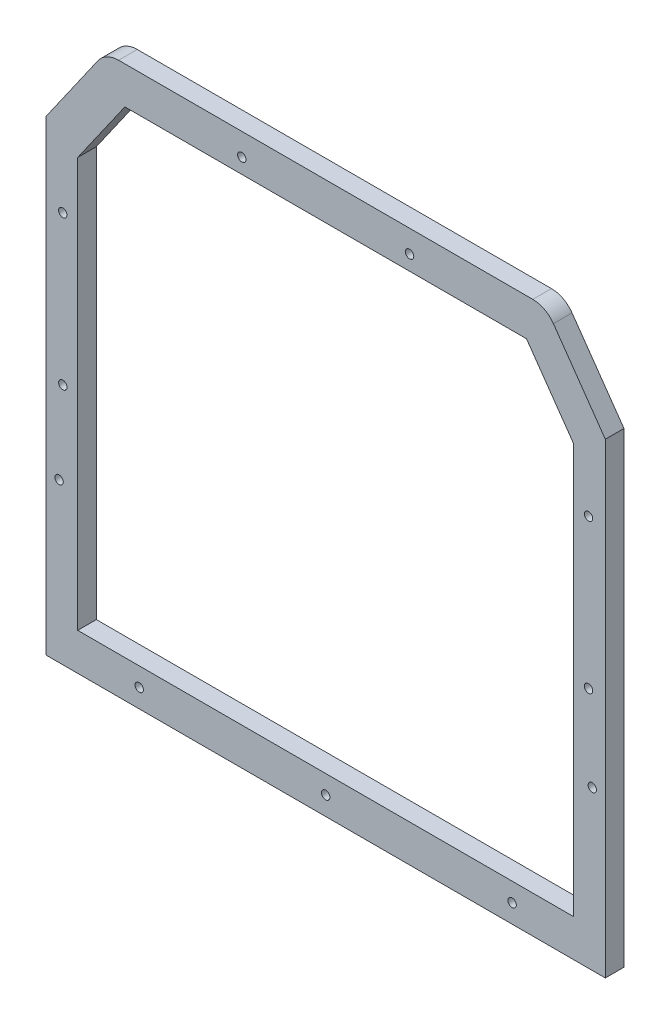
SolidWorks part; units mm, degrees
material "ABS"
ref_plane "Alzado" through (0, 0, 0) normal (0, 0, 1) x (1, 0, 0)
ref_plane "Planta" through (0, 0, 0) normal (0, 1, 0) x (1, 0, 0)
ref_plane "Vista lateral" through (0, 0, 0) normal (1, 0, 0) x (0, 0, -1)
sketch "Croquis1" plane through (0, 0, 0) normal (0, 0, 1) x (1, 0, 0)
  line L0 (303.5586, 129.4867) -> (275.1559, 170.0499)
  line L1 (264.0973, 175.8067) -> (41.9027, 175.8067)
  line L2 (30.8441, 170.0499) -> (2.4414, 129.4867)
  line L3 (0, 121.7435) -> (0, 0)
  line L5 (20, 0) -> (20, 119.694)
  line L6 (20, 119.694) -> (45.2863, 155.8067)
  line L7 (45.2863, 155.8067) -> (260.7137, 155.8067)
  line L8 (260.7137, 155.8067) -> (286, 119.694)
  line L9 (286, 119.694) -> (286, 0)
  line L11 (306, 0) -> (306, 121.7435)
  line L12 (0, 0) -> (0, -120)
  line L13 (0, -120) -> (306, -120)
  line L14 (306, -120) -> (306, 0)
  line L15 (20, 0) -> (20, -100)
  line L16 (20, -100) -> (286, -100)
  line L17 (286, -100) -> (286, 0)
  arc A0 (306, 121.7435) -> (303.5586, 129.4867) centre (292.5, 121.7435) ccw
  arc A1 (275.1559, 170.0499) -> (264.0973, 175.8067) centre (264.0973, 162.3067) ccw
  arc A2 (41.9027, 175.8067) -> (30.8441, 170.0499) centre (41.9027, 162.3067) ccw
  arc A3 (2.4414, 129.4867) -> (0, 121.7435) centre (13.5, 121.7435) ccw
  dimension "D5" = 13.5
  dimension "D6" = 13.5
  dimension "D7" = 20
  dimension "D1" = 222.1947
  dimension "D2" = 306
  dimension "D3" = 121.7435
  dimension "D4" = 54.0632
  dimension "D8" = 20
  dimension "D9" = 20
  dimension "D10" = 20
  dimension "D11" = 20
  dimension "D12" = 28.4027
  dimension "D13" = 30.8441
  dimension "D14" = 20
  dimension "D15" = 125
  dimension "D16" = 222.1947
  dimension "D17" = 120
extrude "Saliente-Extruir1" add sketch "Croquis1" along normal blind 10
sketch "Croquis2" plane through (0, 0, 10) normal (0, 0, 1) x (1, 0, 0)
  line L0 (108, 163.8067) -> (198, 163.8067) construction
  line L1 (264.0973, 175.8067) -> (41.9027, 175.8067) construction
  line L2 (260.7137, 155.8067) -> (45.2863, 155.8067) construction
  line L3 (20, 119.694) -> (20, -100) construction
  line L4 (286, -100) -> (286, 119.694) construction
  line L5 (0, 50) -> (306, 50) construction
  line L6 (0, 121.7435) -> (0, -120) construction
  line L7 (306, -120) -> (306, 121.7435) construction
  circle A0 centre (108, 163.8067) radius 2.25
  circle A1 centre (198, 163.8067) radius 2.25
  circle A2 centre (12, 10) radius 2.25
  circle A3 centre (294, 10) radius 2.25
  circle A4 centre (294, 90) radius 2.25
  circle A5 centre (12, 90) radius 2.25
  point P4 (153, 163.8067)
  point P12 (153, 175.8067)
  dimension "D1" = 4.5
  dimension "D2" = 4.5
  dimension "D4" = 4.5
  dimension "D5" = 4.5
  dimension "D6" = 8
  dimension "D9" = 8
  dimension "D3" = 90
  dimension "D7" = 10
  dimension "D8" = 8
  dimension "D10" = 50
extrude "Cortar-Extruir1" cut sketch "Croquis2" against normal through all
sketch "Croquis3" plane through (0, 0, 10) normal (0, 0, 1) x (1, 0, 0)
  line L0 (10, -35) -> (296, -35) construction
  line L1 (260.7137, 155.8067) -> (45.2863, 155.8067) construction
  line L2 (53, -110) -> (153, -110) construction
  line L3 (153, -110) -> (253, -110) construction
  line L4 (0, 121.7435) -> (0, -120) construction
  line L5 (20, -100) -> (286, -100) construction
  circle A0 centre (10, -35) radius 2.25
  circle A1 centre (296, -35) radius 2.25
  circle A2 centre (53, -110) radius 2.25
  circle A3 centre (153, -110) radius 2.25
  circle A4 centre (253, -110) radius 2.25
  point P11 (153, -35)
  point P14 (153, 155.8067)
  dimension "D1" = 4.5
  dimension "D2" = 10
  dimension "D3" = 100
  dimension "D4" = 10
  dimension "D5" = 65
extrude "Cortar-Extruir2" cut sketch "Croquis3" against normal blind 10
sketch "Croquis4" plane through (0, 0, 10) normal (0, 0, 1) x (1, 0, 0)
  line L0 (0, 121.7435) -> (0, -120) construction
  line L1 (3, 206.3553) -> (303, 206.3553)
  line L2 (3, 206.3553) -> (3, -140.5633)
  line L3 (3, -140.5633) -> (303, -140.5633)
  line L4 (303, 206.3553) -> (303, -140.5633)
  line L5 (306, -120) -> (306, 121.7435) construction
  dimension "D1" = 3
  dimension "D2" = 3
extrude "Cortar-Extruir3" cut sketch "Croquis4" against normal blind 10 flip side to cut
